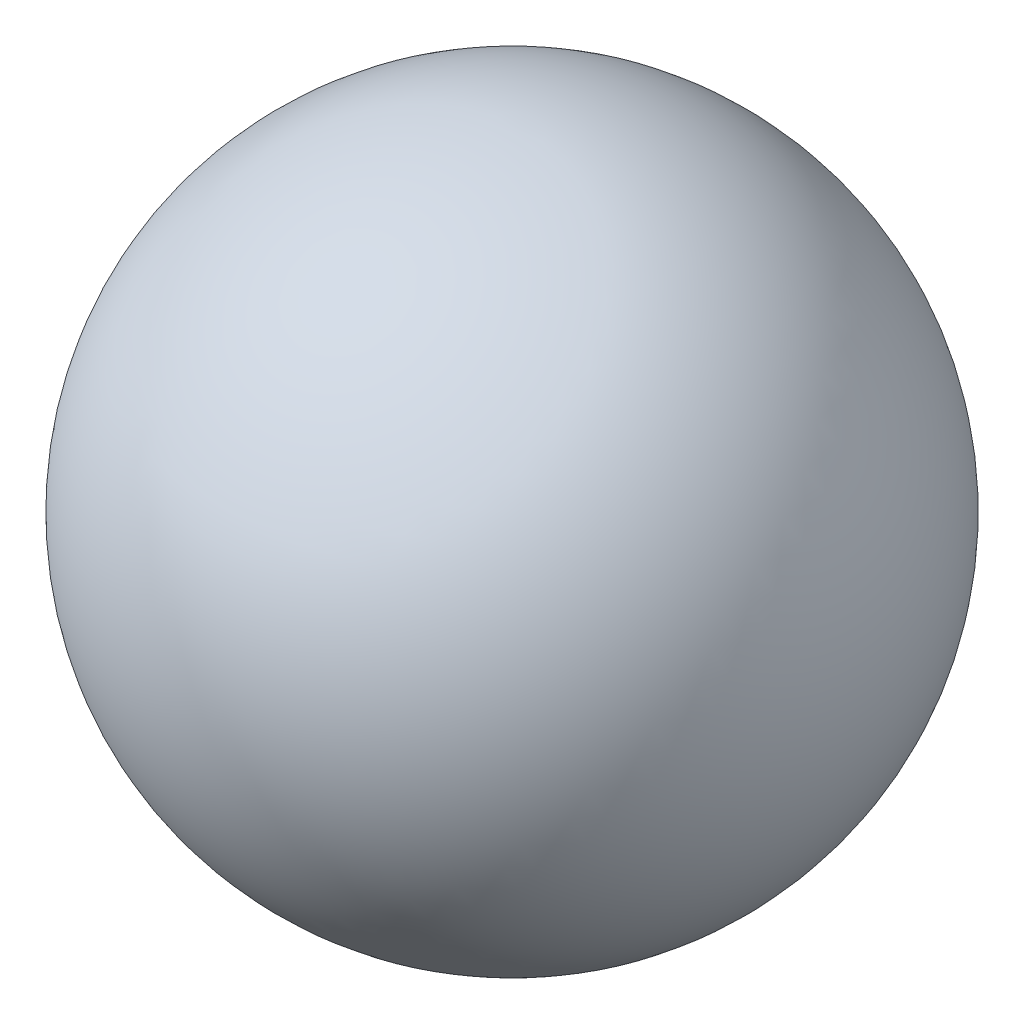
SolidWorks part; units mm, degrees
ref_plane "Front Plane" through (0, 0, 0) normal (0, 0, 1) x (1, 0, 0)
ref_plane "Top Plane" through (0, 0, 0) normal (0, 1, 0) x (1, 0, 0)
ref_plane "Right Plane" through (0, 0, 0) normal (1, 0, 0) x (0, 0, -1)
sketch "Sketch1" plane through (0, 0, 0) normal (0, 0, 1) x (1, 0, 0)
  line L0 (0, 105.0842) -> (0, -101.9811) construction
  line L1 (0, 80) -> (0, 76)
  line L2 (0, -76) -> (0, -80)
  line L3 (0, 76) -> (0, -76)
  arc A0 (0, 80) -> (0, -80) centre (0, 0) ccw
  dimension "D1" = 80
revolve "Revolve1" add sketch "Sketch1" angle 360 about L0
